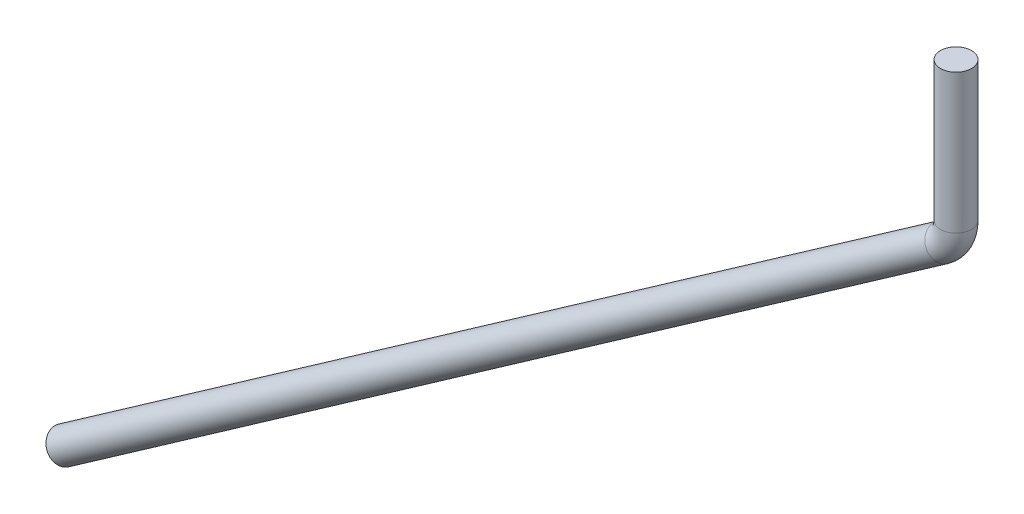
SolidWorks part; units mm, degrees
ref_plane "Front Plane" through (0, 0, 0) normal (0, 0, 1) x (1, 0, 0)
ref_plane "Top Plane" through (0, 0, 0) normal (0, 1, 0) x (1, 0, 0)
ref_plane "Right Plane" through (0, 0, 0) normal (1, 0, 0) x (0, 0, -1)
sketch "Sketch1" plane through (0, 0, 0) normal (0, 0, 1) x (1, 0, 0)
  line L0 (0, 0) -> (0, -1.1378)
  line L1 (-0.1083, -1.3458) -> (-7.2823, -6.3691)
  arc A0 (0, -1.1378) -> (-0.1083, -1.3458) centre (-0.254, -1.1378) cw
  circle A1 centre (3.6106, 6.4894) radius 0.127
  point P6 (0, -1.27)
  dimension "D4" = 0.254
  dimension "D5" = 0.254
  dimension "D1" = 125
  dimension "D2" = 1.27
  dimension "D3" = 8.89
sweep "Sweep1" add path "Sketch1" circular profile diameter 0.254 parameters "D3"=0.254
